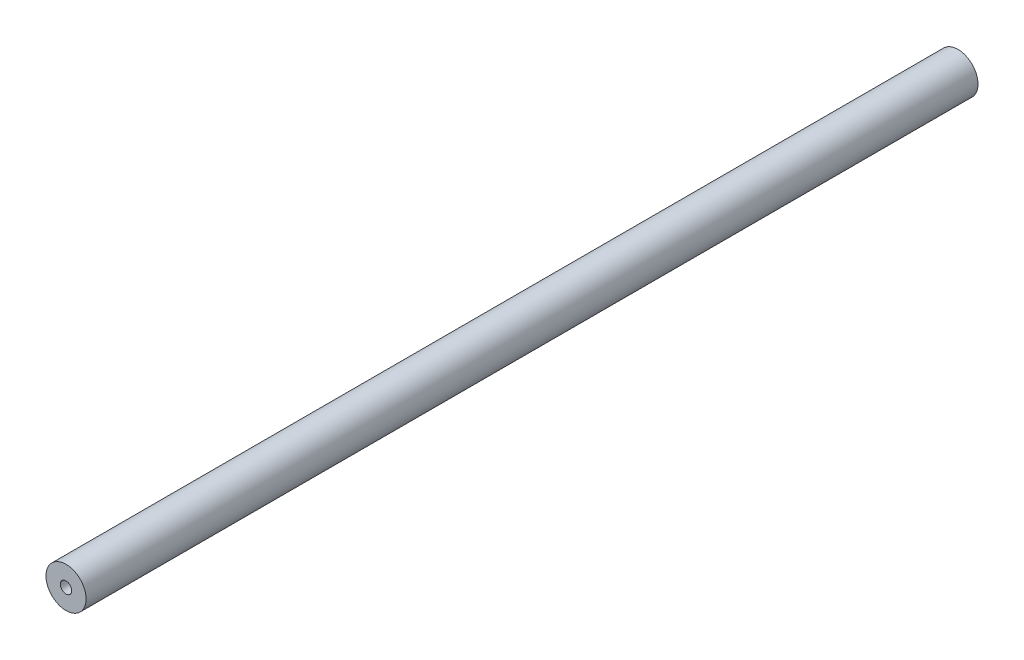
SolidWorks part; units mm, degrees
ref_plane "Front Plane" through (0, 0, 0) normal (0, 0, 1) x (1, 0, 0)
ref_plane "Top Plane" through (0, 0, 0) normal (0, 1, 0) x (1, 0, 0)
ref_plane "Right Plane" through (0, 0, 0) normal (1, 0, 0) x (0, 0, -1)
sketch "Sketch1" plane through (0, 0, 0) normal (0, 0, 1) x (1, 0, 0)
  circle A0 centre (0, 0) radius 4
  circle A1 centre (0, 0) radius 1.1303
  dimension "D1" = 8
  dimension "D2" = 2.2606
extrude "Boss-Extrude1" add sketch "Sketch1" along normal blind 177.8
